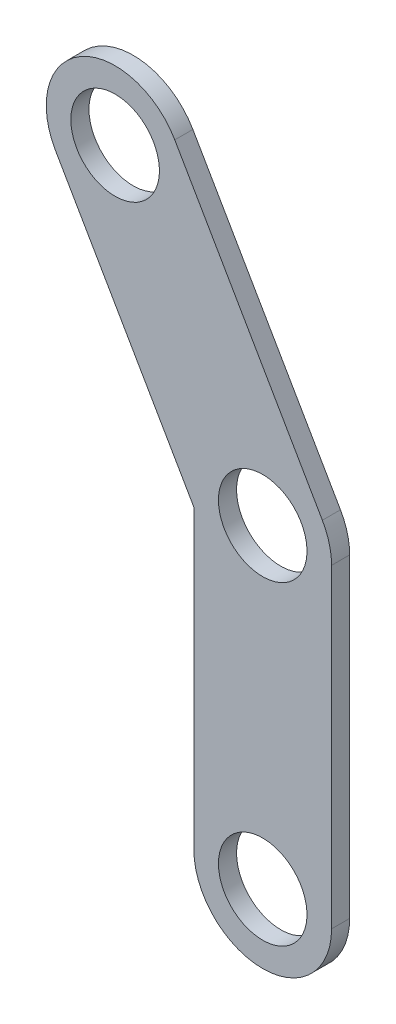
SolidWorks part; units mm, degrees
ref_plane "Front Plane" through (0, 0, 0) normal (0, 0, 1) x (1, 0, 0)
ref_plane "Top Plane" through (0, 0, 0) normal (0, 1, 0) x (1, 0, 0)
ref_plane "Right Plane" through (0, 0, 0) normal (1, 0, 0) x (0, 0, -1)
ref_plane "Plane1" through (0, 0, 0) normal (0, 0, -1) x (-1, 0, 0)
sketch "Sketch1" plane through (0, 0, 0) normal (0, 0, -1) x (-1, 0, 0)
  line L30 (51.5636, 2.0634) -> (51.5636, 103.6634) construction
  line L31 (51.5636, 103.6634) -> (99.1886, 186.1523) construction
  line L32 (29.3386, 2.0634) -> (29.3386, 103.6634)
  line L33 (79.9412, 197.2648) -> (32.3162, 114.7759)
  line L34 (118.436, 175.0398) -> (70.811, 92.5509)
  line L35 (73.7886, 2.0634) -> (73.7886, 110.0134)
  line L36 (51.5636, 103.6634) -> (51.5636, 2.0634) construction
  circle A1 centre (99.1886, 186.1523) radius 14.2875
  circle A7 centre (51.5636, 2.0634) radius 22.225
  circle A8 centre (51.5636, 103.6634) radius 22.225
  circle A9 centre (99.1886, 186.1523) radius 22.225
  circle A10 centre (51.5636, 103.6634) radius 14.2875
  circle A11 centre (51.5636, 2.0634) radius 14.2875
  dimension "D1" = 28.575
  dimension "D2" = 28.575
  dimension "D4" = 210
  dimension "D7" = 44.45
  dimension "D8" = 44.45
  dimension "D9" = 44.45
  dimension "D5" = 101.6
  dimension "D6" = 95.25
extrude "Boss-Extrude1" add sketch "Sketch1" against normal blind 5.842
